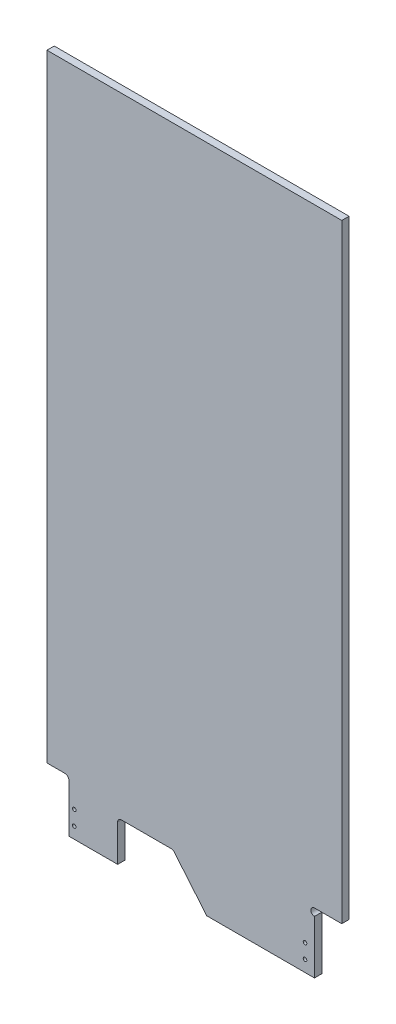
SolidWorks part; units mm, degrees
material "Maple"
ref_plane "Front Plane" through (0, 0, 0) normal (0, 0, 1) x (1, 0, 0)
ref_plane "Top Plane" through (0, 0, 0) normal (0, 1, 0) x (1, 0, 0)
ref_plane "Right Plane" through (0, 0, 0) normal (1, 0, 0) x (0, 0, -1)
sketch "Sketch1" plane through (0, 0, 0) normal (0, 0, 1) x (1, 0, 0)
  line L0 (10443.2333, 13331.6551) -> (10455.9847, 13336.0691)
  line L1 (10447.1279, 13320.4039) -> (10459.8794, 13324.8178)
  line L2 (10695.1971, 13320.4039) -> (10682.4456, 13324.8178)
  line L3 (10699.0917, 13331.6551) -> (10686.3403, 13336.0691)
  line L4 (10541.0517, 13397.9519) -> (10528.4971, 13396.0356)
  line L5 (10526.6882, 13397.3654) -> (10521.8975, 13428.7519)
  line L6 (10537.5908, 13431.1472) -> (10542.3815, 13399.7607)
  line L7 (10736.3381, 13352.0402) -> (10736.3381, 13308.8602)
  line L8 (10731.7661, 13352.0402) -> (10731.7661, 13308.8602)
  line L9 (10778.248, 13352.0402) -> (10778.248, 13308.8602)
  line L10 (10773.676, 13352.0402) -> (10773.676, 13308.8602)
  line L11 (10615.3515, 13397.3654) -> (10620.1422, 13428.7519)
  line L12 (10604.4489, 13431.1472) -> (10599.6582, 13399.7607)
  line L13 (10491.3092, 13387.9533) -> (10481.8376, 13418.2575)
  line L14 (10577.5117, 13434.6656) -> (10564.8117, 13434.6722)
  line L15 (10650.7305, 13387.9533) -> (10660.2022, 13418.2575)
  line L16 (10523.2273, 13430.5607) -> (10535.7819, 13432.477)
  line L17 (10564.7937, 13399.7472) -> (10577.4937, 13399.7407)
  line L18 (10496.9897, 13422.9934) -> (10506.4614, 13392.6891)
  line L19 (10636.62, 13390.7003) -> (10648.7417, 13386.9116)
  line L20 (10645.05, 13422.9934) -> (10635.5783, 13392.6891)
  line L21 (10563.2233, 13433.0855) -> (10563.207, 13401.3355)
  line L22 (10579.082, 13401.3273) -> (10579.0983, 13433.0773)
  line L23 (10482.8792, 13420.2463) -> (10495.0009, 13424.035)
  line L24 (10505.4197, 13390.7003) -> (10493.298, 13386.9116)
  line L25 (10823.5812, 13165.8355) -> (10823.5812, 13122.6555)
  line L26 (10819.0092, 13165.8355) -> (10819.0092, 13122.6555)
  line L27 (10618.8124, 13430.5607) -> (10606.2578, 13432.477)
  line L28 (10600.988, 13397.9519) -> (10613.5426, 13396.0356)
  line L29 (10659.1605, 13420.2463) -> (10647.0388, 13424.035)
  line L30 (10461.2028, 13017.5001) -> (10461.2028, 13081.5947)
  line L31 (10559.6499, 13085.667) -> (10616.6252, 13017.5001)
  line L32 (10467.5528, 13087.9447) -> (10554.7777, 13087.9447)
  line L33 (10604.6398, 13059.119) -> (10650.0487, 13080.9819)
  line L34 (10597.0129, 13060.7681) -> (10579.755, 13081.4159)
  line L35 (10633.2213, 13115.9323) -> (10581.8726, 13091.2096)
  line L36 (10653.0155, 13089.4579) -> (10641.6974, 13112.9655)
  line L37 (10776.2577, 13185.5577) -> (10728.0783, 13162.3608)
  line L38 (10725.8532, 13156.0038) -> (10738.5668, 13129.5979)
  line L39 (10795.3283, 13156.9268) -> (10782.6147, 13183.3327)
  line L40 (10744.9239, 13127.3729) -> (10793.1033, 13150.5697)
  line L41 (10616.6252, 13017.5001) -> (10804.5257, 13017.5001)
  line L42 (10804.5257, 13110.5905) -> (10804.5257, 13017.5001)
  line L43 (10804.5257, 13123.2905) -> (10852.1507, 13123.2905)
  line L44 (10337.8007, 14185.9001) -> (10337.8021, 13109.003)
  line L45 (10852.1479, 14185.9001) -> (10852.1507, 13123.2905)
  line L46 (10375.9021, 13017.5001) -> (10461.2028, 13017.5001)
  line L47 (10337.8007, 14185.9001) -> (10852.1479, 14185.9001)
  line L48 (10375.9021, 13017.5001) -> (10375.9021, 13102.653)
  line L49 (10369.5521, 13109.003) -> (10337.8021, 13109.003)
  line L50 (10368.649, 13352.5482) -> (10368.649, 13309.3682)
  line L51 (10364.077, 13352.5482) -> (10364.077, 13309.3682)
  line L52 (10410.6461, 13352.5482) -> (10410.6461, 13309.3682)
  line L53 (10406.0741, 13352.5482) -> (10406.0741, 13309.3682)
  circle A0 centre (10675.1245, 13279.1384) radius 2.0955
  circle A1 centre (10444.8254, 13353.4836) radius 5.9531
  circle A2 centre (10461.8744, 13304.2311) radius 5.9531
  arc A3 (10459.8794, 13324.8178) -> (10455.9847, 13336.0691) centre (10457.932, 13330.4435) ccw
  arc A4 (10443.2333, 13331.6551) -> (10447.1279, 13320.4039) centre (10445.1806, 13326.0295) ccw
  circle A5 centre (10680.4506, 13304.2311) radius 5.9531
  circle A6 centre (10697.4996, 13353.4836) radius 5.9531
  arc A7 (10686.3403, 13336.0691) -> (10682.4456, 13324.8178) centre (10684.393, 13330.4435) ccw
  arc A8 (10695.1971, 13320.4039) -> (10699.0917, 13331.6551) centre (10697.1444, 13326.0295) ccw
  circle A9 centre (10344.1507, 13550.9001) radius 1.5875
  circle A10 centre (10344.1507, 13703.3001) radius 1.5875
  circle A11 centre (10344.1507, 14008.1001) radius 1.5875
  circle A12 centre (10344.1507, 13855.7001) radius 1.5875
  circle A13 centre (10399.3957, 14179.2527) radius 1.5875
  circle A14 centre (10344.1507, 14160.5001) radius 1.5875
  circle A15 centre (10845.8007, 13550.9001) radius 1.5875
  circle A16 centre (10798.187, 13550.9001) radius 1.5875
  circle A17 centre (10845.8007, 13703.3001) radius 1.5875
  circle A18 centre (10845.8007, 13855.7001) radius 1.5875
  circle A19 centre (10845.8007, 14008.1001) radius 1.5875
  circle A20 centre (10692.7657, 14179.2527) radius 1.5875
  circle A21 centre (10594.9757, 14179.2527) radius 1.5875
  circle A22 centre (10497.1857, 14179.2527) radius 1.5875
  circle A23 centre (10845.7979, 14160.5001) radius 1.5875
  circle A24 centre (10790.5557, 14179.2527) radius 1.5875
  circle A25 centre (10755.007, 13352.2942) radius 2.0955
  circle A26 centre (10708.8263, 13376.4992) radius 2.0955
  circle A27 centre (10708.8263, 13302.174) radius 2.0955
  arc A28 (10731.7661, 13308.8602) -> (10736.3381, 13308.8602) centre (10734.0521, 13308.8602) ccw
  arc A29 (10736.3381, 13352.0402) -> (10731.7661, 13352.0402) centre (10734.0521, 13352.0402) ccw
  arc A30 (10773.676, 13308.8602) -> (10778.248, 13308.8602) centre (10775.962, 13308.8602) ccw
  arc A31 (10778.248, 13352.0402) -> (10773.676, 13352.0402) centre (10775.962, 13352.0402) ccw
  circle A32 centre (10467.2005, 13279.1384) radius 2.0955
  circle A33 centre (10734.0521, 13398.9488) radius 11.1125
  circle A34 centre (10775.962, 13398.9364) radius 11.1125
  circle A35 centre (10467.9679, 13213.2533) radius 2.0955
  circle A36 centre (10674.3571, 13213.2533) radius 2.0955
  circle A37 centre (10708.3278, 13236.4728) radius 2.0955
  circle A38 centre (10742.2986, 13259.6923) radius 2.0955
  circle A39 centre (10571.0767, 13352.8133) radius 11.1125
  circle A40 centre (10571.0199, 13218.5702) radius 17.4625
  circle A41 centre (10571.0813, 13317.8883) radius 11.1125
  circle A42 centre (10571.086, 13282.9633) radius 11.1125
  circle A43 centre (10665.5741, 13083.9291) radius 2.159
  circle A44 centre (10644.7487, 13126.7595) radius 2.159
  circle A45 centre (10713.2773, 13160.0802) radius 2.159
  circle A46 centre (10747.5416, 13176.7405) radius 2.159
  circle A47 centre (10793.7362, 13135.3438) radius 1.1303
  arc A48 (10823.5812, 13165.8355) -> (10819.0092, 13165.8355) centre (10821.2952, 13165.8355) ccw
  arc A49 (10819.0092, 13122.6555) -> (10823.5812, 13122.6555) centre (10821.2952, 13122.6555) ccw
  circle A50 centre (10488.1149, 13199.4826) radius 6.35
  circle A51 centre (10654.2101, 13199.4826) radius 6.35
  circle A52 centre (10755.007, 13368.1412) radius 3.1115
  circle A53 centre (10845.8007, 13246.1001) radius 1.5875
  circle A54 centre (10796.8058, 13309.9208) radius 1.5875
  circle A55 centre (10796.8058, 13247.433) radius 1.5875
  circle A56 centre (10691.9754, 13290.6562) radius 5.9531
  circle A57 centre (10708.8263, 13339.3366) radius 5.9531
  circle A58 centre (10845.8007, 13398.5001) radius 1.5875
  circle A59 centre (10798.187, 13398.5001) radius 1.5875
  circle A60 centre (10725.3132, 13248.0825) radius 5.9531
  circle A61 centre (10691.29, 13224.8272) radius 5.9531
  circle A62 centre (10400.0264, 13259.6923) radius 2.0955
  circle A63 centre (10433.9972, 13236.4728) radius 2.0955
  arc A64 (10559.6499, 13085.667) -> (10554.7777, 13087.9447) centre (10554.7777, 13081.5947) ccw
  arc A65 (10467.5528, 13087.9447) -> (10461.2028, 13081.5947) centre (10467.5528, 13081.5947) ccw
  arc A66 (10597.0129, 13060.7681) -> (10604.6398, 13059.119) centre (10601.8851, 13064.8404) ccw
  arc A67 (10581.8726, 13091.2096) -> (10579.755, 13081.4159) centre (10584.6273, 13085.4882) ccw
  arc A68 (10650.0487, 13080.9819) -> (10653.0155, 13089.4579) centre (10647.2941, 13086.7033) ccw
  arc A69 (10641.6974, 13112.9655) -> (10633.2213, 13115.9323) centre (10635.976, 13110.2109) ccw
  arc A70 (10728.0783, 13162.3608) -> (10725.8532, 13156.0038) centre (10730.1443, 13158.0698) ccw
  arc A71 (10793.1033, 13150.5697) -> (10795.3283, 13156.9268) centre (10791.0373, 13154.8608) ccw
  arc A72 (10782.6147, 13183.3327) -> (10776.2577, 13185.5577) centre (10778.3237, 13181.2667) ccw
  arc A73 (10738.5668, 13129.5979) -> (10744.9239, 13127.3729) centre (10742.8579, 13131.6639) ccw
  circle A74 centre (10788.0151, 13037.3121) radius 3.1115
  circle A75 centre (10788.0151, 13062.7121) radius 3.1115
  circle A76 centre (10793.7362, 13135.3438) radius 1.1303
  circle A77 centre (10781.6651, 13097.6371) radius 3.1115
  circle A78 centre (10845.8007, 13147.103) radius 1.5875
  arc A79 (10804.5257, 13123.2905) -> (10804.5257, 13110.5905) centre (10804.5257, 13116.9405) ccw
  circle A80 centre (10391.7751, 13097.6371) radius 3.1115
  arc A81 (10375.9021, 13102.653) -> (10369.5521, 13109.003) centre (10369.5521, 13102.653) ccw
  circle A82 centre (10344.1521, 13147.103) radius 1.5875
  circle A83 centre (10385.4251, 13062.7121) radius 3.1115
  circle A84 centre (10385.4251, 13037.3121) radius 3.1115
  circle A85 centre (10387.318, 13368.1412) radius 3.1115
  circle A86 centre (10344.1507, 13398.5001) radius 1.5875
  circle A87 centre (10344.1507, 13246.1001) radius 1.5875
  circle A88 centre (10450.3496, 13290.6562) radius 5.9531
  circle A89 centre (10433.4987, 13339.3366) radius 5.9531
  circle A90 centre (10417.0118, 13248.0825) radius 5.9531
  circle A91 centre (10451.035, 13224.8272) radius 5.9531
  circle A92 centre (10408.3601, 13399.1233) radius 11.1125
  circle A93 centre (10366.363, 13399.1466) radius 11.1125
  arc A94 (10364.077, 13309.3682) -> (10368.649, 13309.3682) centre (10366.363, 13309.3682) ccw
  arc A95 (10368.649, 13352.5482) -> (10364.077, 13352.5482) centre (10366.363, 13352.5482) ccw
  arc A96 (10406.0741, 13309.3682) -> (10410.6461, 13309.3682) centre (10408.3601, 13309.3682) ccw
  arc A97 (10410.6461, 13352.5482) -> (10406.0741, 13352.5482) centre (10408.3601, 13352.5482) ccw
  circle A98 centre (10433.4987, 13376.4992) radius 2.0955
  circle A99 centre (10433.4987, 13302.174) radius 2.0955
  circle A100 centre (10387.318, 13352.2942) radius 2.0955
  ellipse E0 centre (10637.0935, 13392.2155) end of major axis (10636.62, 13390.7003) minor radius 1.5875 (10635.5783, 13392.6891) -> (10636.62, 13390.7003) ccw
  ellipse E1 centre (10536.0215, 13430.9077) end of major axis (10537.5908, 13431.1472) minor radius 1.5875 (10537.5908, 13431.1472) -> (10535.7819, 13432.477) ccw
  ellipse E2 centre (10523.4669, 13428.9914) end of major axis (10523.2273, 13430.5607) minor radius 1.5875 (10523.2273, 13430.5607) -> (10521.8975, 13428.7519) ccw
  ellipse E3 centre (10540.8122, 13399.5212) end of major axis (10541.0517, 13397.9519) minor radius 1.5875 (10541.0517, 13397.9519) -> (10542.3815, 13399.7607) ccw
  ellipse E4 centre (10528.2576, 13397.6049) end of major axis (10528.018, 13399.1742) minor radius 1.5875 (10526.6882, 13397.3654) -> (10528.4971, 13396.0356) ccw
  ellipse E5 centre (10618.5728, 13428.9914) end of major axis (10618.8124, 13430.5607) minor radius 1.5875 (10620.1422, 13428.7519) -> (10618.8124, 13430.5607) ccw
  ellipse E6 centre (10601.2276, 13399.5212) end of major axis (10600.988, 13397.9519) minor radius 1.5875 (10599.6582, 13399.7607) -> (10600.988, 13397.9519) ccw
  ellipse E7 centre (10606.0182, 13430.9077) end of major axis (10604.4489, 13431.1472) minor radius 1.5875 (10606.2578, 13432.477) -> (10604.4489, 13431.1472) ccw
  ellipse E8 centre (10495.4745, 13422.5198) end of major axis (10496.9897, 13422.9934) minor radius 1.5875 (10496.9897, 13422.9934) -> (10495.0009, 13424.035) ccw
  ellipse E9 centre (10564.8108, 13433.0847) end of major axis (10563.2233, 13433.0855) minor radius 1.5875 (10564.8117, 13434.6722) -> (10563.2233, 13433.0855) ccw
  ellipse E10 centre (10658.6869, 13418.7311) end of major axis (10659.1605, 13420.2463) minor radius 1.5875 (10660.2022, 13418.2575) -> (10659.1605, 13420.2463) ccw
  ellipse E11 centre (10577.5108, 13433.0781) end of major axis (10577.5117, 13434.6656) minor radius 1.5875 (10579.0983, 13433.0773) -> (10577.5117, 13434.6656) ccw
  ellipse E12 centre (10564.7945, 13401.3347) end of major axis (10564.7937, 13399.7472) minor radius 1.5875 (10563.207, 13401.3355) -> (10564.7937, 13399.7472) ccw
  ellipse E13 centre (10492.8244, 13388.4268) end of major axis (10492.3509, 13389.942) minor radius 1.5875 (10491.3092, 13387.9533) -> (10493.298, 13386.9116) ccw
  ellipse E14 centre (10649.2153, 13388.4268) end of major axis (10649.6888, 13389.942) minor radius 1.5875 (10648.7417, 13386.9116) -> (10650.7305, 13387.9533) ccw
  ellipse E15 centre (10613.7821, 13397.6049) end of major axis (10614.0217, 13399.1742) minor radius 1.5875 (10613.5426, 13396.0356) -> (10615.3515, 13397.3654) ccw
  ellipse E16 centre (10483.3528, 13418.7311) end of major axis (10482.8792, 13420.2463) minor radius 1.5875 (10482.8792, 13420.2463) -> (10481.8376, 13418.2575) ccw
  ellipse E17 centre (10734.1028, 13117.2498) end of major axis (10731.9463, 13117.3544) minor radius 2.159
  ellipse E18 centre (10768.3671, 13133.9102) end of major axis (10766.2106, 13134.0147) minor radius 2.159
  ellipse E19 centre (10623.9467, 13116.645) end of major axis (10622.362, 13116.7419) minor radius 1.5877
  ellipse E20 centre (10599.0864, 13051.6008) end of major axis (10597.5017, 13051.6977) minor radius 1.5877
  ellipse E21 centre (10644.7722, 13073.8146) end of major axis (10643.1875, 13073.9115) minor radius 1.5877
  ellipse E22 centre (10669.6325, 13138.8588) end of major axis (10669.7294, 13140.4435) minor radius 1.5877
  ellipse E23 centre (10646.5652, 13422.5198) end of major axis (10645.05, 13422.9934) minor radius 1.5875 (10647.0388, 13424.035) -> (10645.05, 13422.9934) ccw
  ellipse E24 centre (10577.4945, 13401.3282) end of major axis (10577.4953, 13402.9157) minor radius 1.5875 (10577.4937, 13399.7407) -> (10579.082, 13401.3273) ccw
  ellipse E25 centre (10504.9462, 13392.2155) end of major axis (10505.4197, 13390.7003) minor radius 1.5875 (10505.4197, 13390.7003) -> (10506.4614, 13392.6891) ccw
sketch "Sketch2" plane through (0, 0, 0) normal (0, 0, 1) x (1, 0, 0)
  line L0 (10375.9021, 13017.5001) -> (10461.2028, 13017.5001)
  line L1 (10461.2028, 13017.5001) -> (10461.2028, 13081.5947)
  line L2 (10467.5528, 13087.9447) -> (10554.7777, 13087.9447)
  line L3 (10559.6499, 13085.667) -> (10616.6252, 13017.5001)
  line L4 (10616.6252, 13017.5001) -> (10804.5257, 13017.5001)
  line L5 (10804.5257, 13017.5001) -> (10804.5257, 13110.5905)
  line L6 (10804.5257, 13123.2905) -> (10852.1507, 13123.2905)
  line L7 (10852.1507, 13123.2905) -> (10852.1479, 14185.9001)
  line L8 (10852.1479, 14185.9001) -> (10337.8007, 14185.9001)
  line L9 (10337.8007, 14185.9001) -> (10337.8021, 13109.003)
  line L10 (10337.8021, 13109.003) -> (10369.5521, 13109.003)
  line L11 (10375.9021, 13102.653) -> (10375.9021, 13017.5001)
  arc A0 (10461.2028, 13081.5947) -> (10467.5528, 13087.9447) centre (10467.5528, 13081.5947) cw
  arc A1 (10554.7777, 13087.9447) -> (10559.6499, 13085.667) centre (10554.7777, 13081.5947) cw
  arc A2 (10369.5521, 13109.003) -> (10375.9021, 13102.653) centre (10369.5521, 13102.653) cw
  arc A3 (10804.5257, 13123.2905) -> (10804.5257, 13110.5905) centre (10804.5257, 13116.9405) ccw
extrude "Extrude1" add sketch "Sketch2" against normal blind 12.7
sketch "Sketch3" plane through (0, 0, 0) normal (0, 0, 1) x (1, 0, 0)
  circle A0 centre (10385.4251, 13062.7121) radius 3.1115
  circle A1 centre (10385.4251, 13037.3121) radius 3.1115
  circle A2 centre (10788.0151, 13062.7121) radius 3.1115
  circle A3 centre (10788.0151, 13037.3121) radius 3.1115
extrude "Cut-Extrude1" cut sketch "Sketch3" against normal up to surface (12.7 mm away) up to face at (10564.3593, 13216.6221, -12.7)
